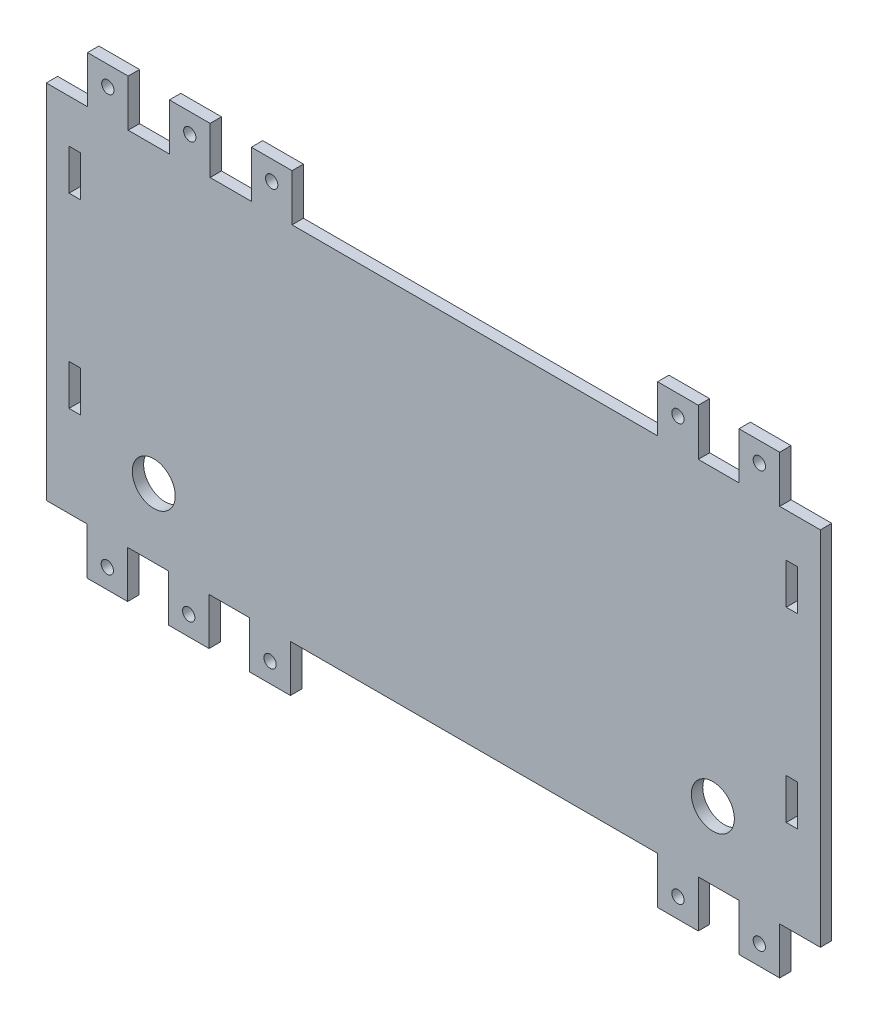
SolidWorks part; units mm, degrees
ref_plane "Front Plane" through (0, 0, 0) normal (0, 0, 1) x (1, 0, 0)
ref_plane "Top Plane" through (0, 0, 0) normal (0, 1, 0) x (1, 0, 0)
ref_plane "Right Plane" through (0, 0, 0) normal (1, 0, 0) x (0, 0, -1)
sketch "Sketch1" plane through (0, 0, 0) normal (0, 0, 1) x (1, 0, 0)
  line L1 (-47.7778, 29.4444) -> (168.1222, 29.4444)
  line L2 (-47.7778, 29.4444) -> (-47.7778, -97.5556)
  line L3 (-47.7778, -97.5556) -> (168.1222, -97.5556)
  line L4 (168.1222, 29.4444) -> (168.1222, -97.5556)
  dimension "D1" = 127
  dimension "D2" = 215.9
extrude "Boss-Extrude1" add sketch "Sketch1" along normal blind 3.175
sketch "Sketch4" plane through (0, 0, 0) normal (0, 0, -1) x (-1, 0, 0)
  line L0 (-168.1222, 29.4444) -> (-156.7722, 29.4444)
  line L1 (-168.1222, 29.4444) -> (-168.1222, 16.3644)
  line L2 (-168.1222, 16.3644) -> (-156.7722, 16.3644)
  line L3 (-156.7722, 29.4444) -> (-156.7722, 16.3644)
  line L4 (-145.4222, 29.4444) -> (-134.0722, 29.4444)
  line L5 (-145.4222, 29.4444) -> (-145.4222, 16.3644)
  line L6 (-145.4222, 16.3644) -> (-134.0722, 16.3644)
  line L7 (-134.0722, 29.4444) -> (-134.0722, 16.3644)
  line L8 (-122.7222, 29.4444) -> (-20.7723, 29.4444)
  line L9 (-122.7222, 29.4444) -> (-122.7222, 16.3644)
  line L10 (-122.7222, 16.3644) -> (-20.7723, 16.3644)
  line L11 (-20.7723, 29.4444) -> (-20.7723, 16.3644)
  line L12 (-9.4223, 29.4444) -> (2.0778, 29.4444)
  line L13 (-9.4223, 29.4444) -> (-9.4223, 16.3644)
  line L14 (-9.4223, 16.3644) -> (2.0778, 16.3644)
  line L15 (2.0778, 29.4444) -> (2.0778, 16.3644)
  line L16 (13.4278, 29.4444) -> (24.9278, 29.4444)
  line L17 (13.4278, 29.4444) -> (13.4278, 16.3644)
  line L18 (13.4278, 16.3644) -> (24.9278, 16.3644)
  line L19 (24.9278, 29.4444) -> (24.9278, 16.3644)
  line L20 (36.2778, 29.4444) -> (47.7778, 29.4444)
  line L21 (36.2778, 29.4444) -> (36.2778, 16.3644)
  line L22 (36.2778, 16.3644) -> (47.7778, 16.3644)
  line L23 (47.7778, 29.4444) -> (47.7778, 16.3644)
  line L24 (47.7778, 29.4444) -> (47.7778, -97.5556) construction
  line L25 (-168.1222, 29.4444) -> (47.7778, 29.4444) construction
  line L28 (-168.1222, -97.5556) -> (-168.1222, 29.4444) construction
  line L30 (-168.1222, -97.5556) -> (-168.1222, 29.4444) construction
  line L31 (-168.1222, -84.4755) -> (-156.7722, -84.4755)
  line L32 (-168.1222, -84.4755) -> (-168.1222, -97.5556)
  line L33 (-168.1222, -97.5556) -> (-156.7722, -97.5556)
  line L34 (-156.7722, -84.4755) -> (-156.7722, -97.5556)
  line L35 (-145.4222, -84.4755) -> (-134.0722, -84.4755)
  line L36 (-145.4222, -84.4755) -> (-145.4222, -97.5556)
  line L37 (-145.4222, -97.5556) -> (-134.0722, -97.5556)
  line L38 (-134.0722, -84.4755) -> (-134.0722, -97.5556)
  line L39 (-122.7222, -84.4755) -> (-20.3222, -84.4755)
  line L40 (-122.7222, -84.4755) -> (-122.7222, -97.5556)
  line L41 (-122.7222, -97.5556) -> (-20.3222, -97.5556)
  line L42 (-20.3222, -84.4755) -> (-20.3222, -97.5556)
  line L43 (-8.9722, -84.4755) -> (2.3778, -84.4755)
  line L44 (-8.9722, -84.4755) -> (-8.9722, -97.5556)
  line L45 (-8.9722, -97.5556) -> (2.3778, -97.5556)
  line L46 (2.3778, -84.4755) -> (2.3778, -97.5556)
  line L47 (13.7278, -84.4755) -> (25.0778, -84.4755)
  line L48 (13.7278, -84.4755) -> (13.7278, -97.5556)
  line L49 (13.7278, -97.5556) -> (25.0778, -97.5556)
  line L50 (25.0778, -84.4755) -> (25.0778, -97.5556)
  line L51 (36.4278, -84.4755) -> (47.7778, -84.4755)
  line L52 (36.4278, -84.4755) -> (36.4278, -97.5556)
  line L53 (36.4278, -97.5556) -> (47.7778, -97.5556)
  line L54 (47.7778, -84.4755) -> (47.7778, -97.5556)
  line L59 (47.7778, -97.5556) -> (-168.1222, -97.5556) construction
  point P29 (-122.7222, -91.0156)
  dimension "D1" = 11.35
  dimension "D2" = 11.35
  dimension "D3" = 11.35
  dimension "D4" = 11.35
  dimension "D5" = 11.35
  dimension "D6" = 13.08
  dimension "D7" = 11.35
  dimension "D8" = 11.35
  dimension "D9" = 11.35
  dimension "D10" = 11.35
  dimension "D11" = 11.35
  dimension "D12" = 13.08
  dimension "D13" = 13.08
  dimension "D14" = 11.35
  dimension "D15" = 45.4
  dimension "D16" = 11.35
  dimension "D17" = 45.4
  dimension "D18" = 11.35
  dimension "D19" = 100.84
extrude "Cut-Extrude1" cut sketch "Sketch4" against normal through all
sketch "Sketch5" plane through (0, 0, 0) normal (0, 0, -1) x (-1, 0, 0)
  line L0 (-134.0722, -84.4755) -> (-145.4222, -84.4755) construction
  line L1 (-168.1222, -84.4755) -> (-168.1222, 16.3644) construction
  line L2 (47.7778, -84.4755) -> (36.4278, -84.4755) construction
  line L3 (47.7778, 16.3644) -> (47.7778, -84.4755) construction
  circle A0 centre (-138.1375, -65.4255) radius 6
  circle A1 centre (17.7931, -65.4255) radius 6
  dimension "D1" = 19.05
  dimension "D3" = 19.05
  dimension "D2" = 29.9847
  dimension "D4" = 29.9847
extrude "Cut-Extrude2" cut sketch "Sketch5" against normal through all both and the other way through all
sketch "Sketch6" plane through (0, 0, 0) normal (0, 0, -1) x (-1, 0, 0)
  line L0 (-156.7722, 29.4444) -> (-145.4222, 29.4444) construction
  line L1 (-134.0722, 29.4444) -> (-122.7222, 29.4444) construction
  line L2 (-168.1222, 16.3644) -> (-156.7722, 16.3644) construction
  line L3 (-20.7723, 29.4444) -> (-9.4223, 29.4444) construction
  line L4 (2.0778, 29.4444) -> (13.4278, 29.4444) construction
  line L5 (24.9278, 29.4444) -> (36.2778, 29.4444) construction
  line L6 (-145.4222, -97.5556) -> (-156.7722, -97.5556) construction
  line L7 (-122.7222, -97.5556) -> (-134.0722, -97.5556) construction
  line L8 (-8.9722, -97.5556) -> (-20.3222, -97.5556) construction
  line L9 (13.7278, -97.5556) -> (2.3778, -97.5556) construction
  line L10 (36.4278, -97.5556) -> (25.0778, -97.5556) construction
  line L11 (-156.7722, -84.4755) -> (-168.1222, -84.4755) construction
  circle A0 centre (-151.0972, 23.9844) radius 1.7145
  circle A1 centre (-128.3972, 23.9844) radius 1.7145
  circle A2 centre (-15.0973, 23.9844) radius 1.7145
  circle A3 centre (7.7528, 23.9844) radius 1.7145
  circle A4 centre (30.6028, 23.9844) radius 1.7145
  circle A6 centre (-128.3972, -92.0955) radius 1.7145
  circle A7 centre (-151.0972, -92.0955) radius 1.7145
  circle A8 centre (-14.6472, -92.0955) radius 1.7145
  circle A9 centre (8.0528, -92.0955) radius 1.7145
  circle A10 centre (30.7528, -92.0955) radius 1.7145
  point P35 (-151.0972, 29.4444)
  point P39 (-128.3972, 29.4444)
  point P43 (-15.0973, 29.4444)
  point P47 (7.7528, 29.4444)
  point P51 (30.6028, 29.4444)
  point P55 (-151.0972, -97.5556)
  point P59 (-128.3972, -97.5556)
  point P63 (-14.6472, -97.5556)
  point P67 (8.0528, -97.5556)
  point P71 (30.7528, -97.5556)
  dimension "D1" = 7.62
  dimension "D2" = 7.62
extrude "Cut-Extrude3" cut sketch "Sketch6" against normal through all
sketch "Sketch10" plane through (0, 0, 3.175) normal (0, 0, 1) x (1, 0, 0)
  line L0 (-47.7778, -84.4755) -> (-36.4278, -84.4755) construction
  line L1 (-41.4278, 4.2644) -> (-38.2528, 4.2644)
  line L2 (-41.4278, 4.2644) -> (-41.4278, -7.0856)
  line L3 (-41.4278, -7.0856) -> (-38.2528, -7.0856)
  line L4 (-38.2528, 4.2644) -> (-38.2528, -7.0856)
  line L5 (-41.4278, -47.7256) -> (-38.2528, -47.7256)
  line L6 (-41.4278, -47.7256) -> (-41.4278, -59.0755)
  line L7 (-41.4278, -59.0755) -> (-38.2528, -59.0755)
  line L8 (-38.2528, -47.7256) -> (-38.2528, -59.0755)
  line L9 (-47.7778, 16.3644) -> (-47.7778, -84.4755) construction
  line L10 (158.5972, 4.2644) -> (161.7722, 4.2644)
  line L11 (158.5972, 4.2644) -> (158.5972, -7.0856)
  line L12 (158.5972, -7.0856) -> (161.7722, -7.0856)
  line L13 (161.7722, 4.2644) -> (161.7722, -7.0856)
  line L14 (158.5972, -47.7256) -> (161.7722, -47.7256)
  line L15 (158.5972, -47.7256) -> (158.5972, -59.0755)
  line L16 (158.5972, -59.0755) -> (161.7722, -59.0755)
  line L17 (161.7722, -47.7256) -> (161.7722, -59.0755)
  line L18 (156.7722, -84.4755) -> (168.1222, -84.4755) construction
  line L19 (168.1222, -84.4755) -> (168.1222, 16.3644) construction
  line L20 (-36.2778, 16.3644) -> (-47.7778, 16.3644) construction
  line L21 (122.7222, 16.3644) -> (20.7723, 16.3644) construction
  line L22 (20.3222, -84.4755) -> (122.7222, -84.4755) construction
  point P20 (160.1847, -59.0755)
  point P23 (162.4472, -84.4755)
  dimension "D1" = 40.64
  dimension "D2" = 25.4
  dimension "D3" = 6.35
  dimension "D4" = 40.64
  dimension "D5" = 25.4
  dimension "D6" = 6.35
  dimension "D7" = 12.1
  dimension "D8" = 100.84
extrude "Cut-Extrude4" cut sketch "Sketch10" against normal blind 3.175
